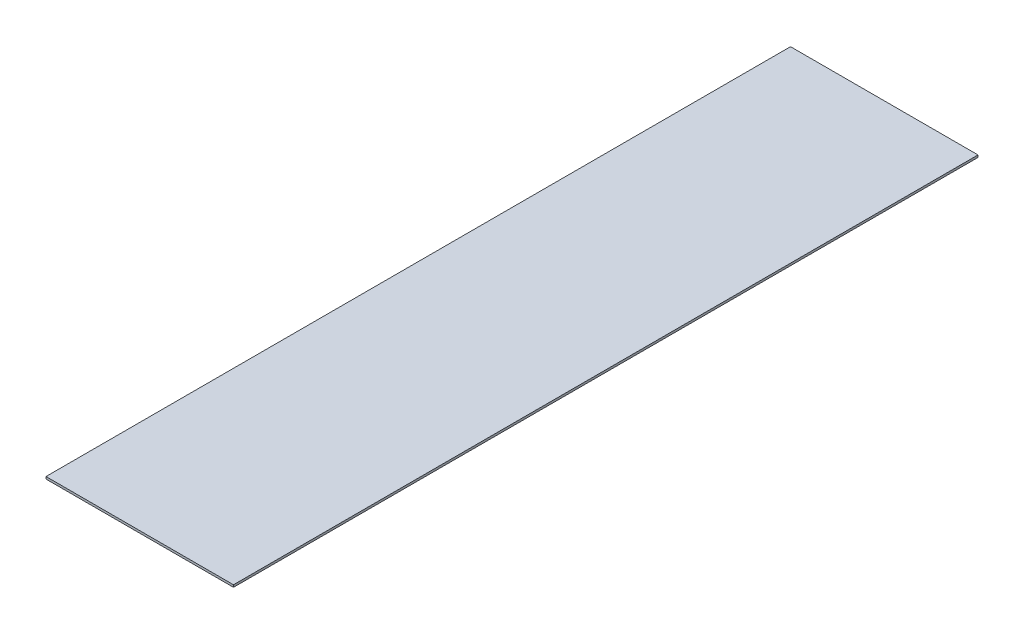
SolidWorks part; units mm, degrees
material "Oak"
ref_plane "Front Plane" through (0, 0, 0) normal (0, 0, 1) x (1, 0, 0)
ref_plane "Top Plane" through (0, 0, 0) normal (0, 1, 0) x (1, 0, 0)
ref_plane "Right Plane" through (0, 0, 0) normal (1, 0, 0) x (0, 0, -1)
sketch "Sketch1" plane through (0, 0, 0) normal (0, 1, 0) x (1, 0, 0)
  line L0 (0, 0) -> (0, 9000) construction
  line L1 (-41.7651, -16.7534) -> (41.7651, 16.7534)
  line L2 (-1000, 4500) -> (-700, 4500) construction
  line L7 (-41.7651, -16.7534) -> (32.6947, -202.376)
  line L8 (41.7651, 16.7534) -> (116.2248, -168.8691)
  line L9 (32.6947, -202.376) -> (116.2248, -168.8691)
  line L10 (-34.5372, -34.772) -> (49.2111, -1.8088)
  line L11 (25.4668, -184.3574) -> (108.7789, -150.3069)
  line L12 (-4.5352, -109.5647) -> (78.995, -76.0579) construction
  line L13 (11486.7647, 4500) -> (-34.5372, -34.772) construction
  line L14 (11486.7647, 4500) -> (25.4668, -184.3574) construction
  arc A0 (0, 0) -> (0, 9000) centre (11486.7647, 4500) cw
  point P1 (0, 0)
  point P4 (0, 9000)
  point P5 (0, 0)
  point P6 (0, 4500)
  point P7 (-700, 4500)
  point P8 (-1000, 4500)
  point P12 (-850, 4500)
  dimension "D8" = 9212.5694
  dimension "D1" = 9000
  dimension "D2" = 1000
  dimension "D3" = 700
  dimension "D4" = 200
  dimension "D5" = 90
  dimension "D6" = 160
  dimension "D7" = 161.1716
  dimension "D9" = 21.857
sketch "Sketch2" plane through (0, 0, 0) normal (0, 1, 0) x (1, 0, 0)
  line L1 (-2097.06, -2727.5223) -> (2097.06, -2727.5223)
  line L2 (-2097.06, -2727.5223) -> (-2097.06, 13927.3312)
  line L3 (-2097.06, 13927.3312) -> (2097.06, 13927.3312)
  line L4 (2097.06, -2727.5223) -> (2097.06, 13927.3312)
  line L5 (0, 5570.299) -> (0, 55570.299) construction
extrude "Boss-Extrude1" add sketch "Sketch2" against normal blind 50
